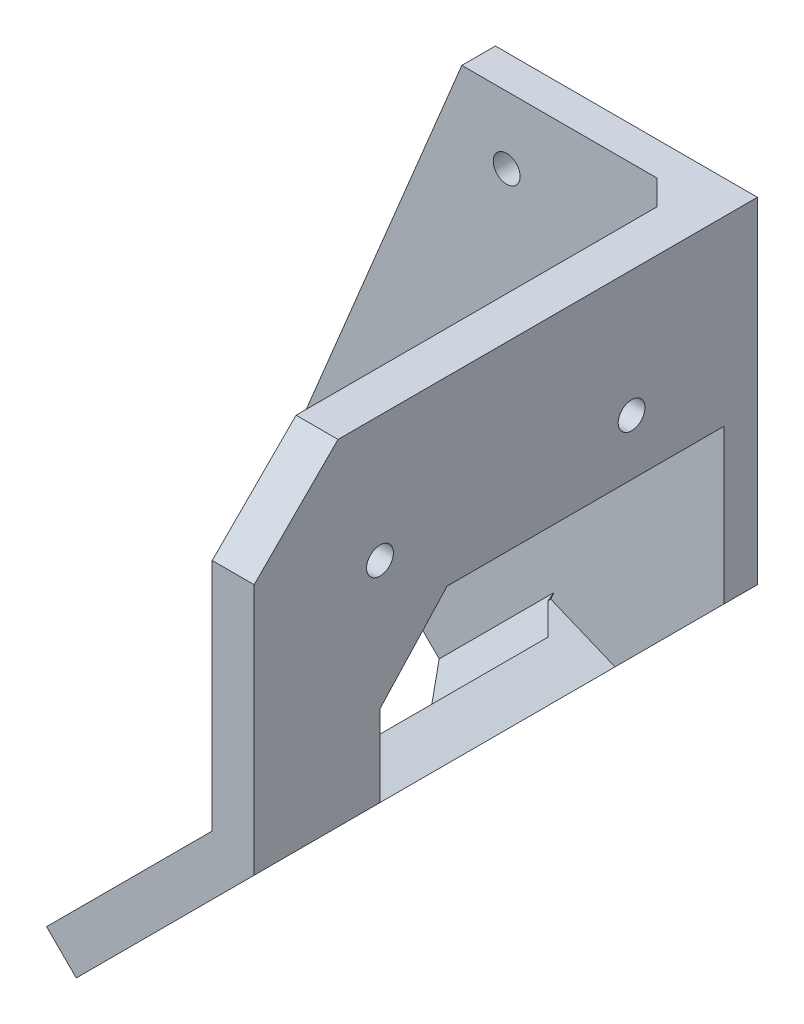
SolidWorks part; units mm, degrees
ref_plane "前视基准面" through (0, 0, 0) normal (0, 0, 1) x (1, 0, 0)
ref_plane "上视基准面" through (0, 0, 0) normal (0, 1, 0) x (1, 0, 0)
ref_plane "右视基准面" through (0, 0, 0) normal (1, 0, 0) x (0, 0, -1)
sketch "Sketch1" plane through (0, 0, 0) normal (0, 0, 1) x (1, 0, 0)
  line L0 (225, -175) -> (225, -135)
  line L2 (220, -135) -> (220, -172.9289)
  line L3 (220, -172.9289) -> (193.1802, -199.7487)
  line L5 (115, -285) -> (225, -175) construction
  line L6 (196.7157, -203.2843) -> (225, -175)
  line L7 (220, -135) -> (225, -135)
  line L8 (196.7157, -203.2843) -> (193.1802, -199.7487)
  dimension "D1" = 5
  dimension "D2" = 5
  dimension "D3" = 40
extrude "Boss-Extrude1" add sketch "Sketch1" along normal blind 60
sketch "Sketch2" plane through (0, 0, 0) normal (0, 0, -1) x (-1, 0, 0)
  line L0 (-225, -135) -> (-193.7596, -135)
  line L1 (-193.7596, -135) -> (-174.6254, -181.194)
  line L2 (-174.6254, -181.194) -> (-196.7157, -203.2843)
  line L3 (-196.7157, -203.2843) -> (-225, -175)
  line L4 (-225, -175) -> (-225, -135)
  line L5 (-225, -135) -> (-220, -135) construction
  circle A0 centre (-207.2895, -167.6641) radius 1.6 construction
  circle A1 centre (-184.0621, -179.3169) radius 1.6 construction
  circle A2 centre (-199.105, -143) radius 1.6 construction
  circle A3 centre (-207.2895, -167.6641) radius 1.6
  circle A4 centre (-184.0621, -179.3169) radius 1.6
  circle A5 centre (-199.105, -143) radius 1.6
  point P17 (-196.7157, -203.2843)
  point P19 (-225, -135)
  dimension "D1" = 50
extrude "Boss-Extrude2" add sketch "Sketch2" against normal blind 4
chamfer "Chamfer1" distance 3 angle 45 2 edges at (206.5901, -186.3388, 4) (220, -153.9645, 4)
sketch "Sketch3" plane through (225, 0, 0) normal (1, 0, 0) x (0, 0, -1)
  line L1 (-60, -175) -> (-60, -135) construction
  line L2 (-60, -135) -> (0, -135) construction
  circle A0 centre (-45, -150) radius 1.6
  circle A1 centre (-15, -150) radius 1.6
  dimension "D1" = 15
  dimension "D2" = 15
  dimension "D3" = 15
  dimension "D4" = 30
  dimension "D5" = 3.2
extrude "Cut-Extrude1" cut sketch "Sketch3" against normal blind 8
sketch "Sketch4" plane through (200, -200, 0) normal (0.7071, -0.7071, 0) x (0, 0, -1)
  line L1 (-60, -4.6447) -> (-60, 35.3553) construction
  line L2 (-60, -4.6447) -> (0, -4.6447) construction
  circle A0 centre (-45, 10.3553) radius 1.6
  circle A1 centre (-15, 10.3553) radius 1.6
  dimension "D1" = 15
  dimension "D2" = 15
  dimension "D3" = 15
  dimension "D4" = 30
  dimension "D5" = 3.2
extrude "Cut-Extrude2" cut sketch "Sketch4" against normal blind 8
chamfer "Chamfer2" distance 10 angle 45 2 edges at (222.5, -135, 60) (194.948, -201.5165, 60)
ref_plane "Plane1" through (239.7792, -99.3198, 0) normal (0.9239, -0.3827, 0) x (0, 0, -1)
sketch "Sketch5" plane through (239.7792, -99.3198, 0) normal (0.9239, -0.3827, 0) x (0, 0, -1)
  line L0 (-37, -58.62) -> (-45, -66.62)
  line L1 (-45, -66.62) -> (-45, -84.5303)
  line L2 (-45, -84.5303) -> (-37, -92.5303)
  line L3 (-37, -92.5303) -> (-4, -92.5303)
  line L4 (-4, -92.5303) -> (-4, -58.62)
  line L5 (-4, -58.62) -> (-37, -58.62)
  line L6 (-50, -38.62) -> (0, -38.62) construction
  line L7 (-50, -112.5303) -> (0, -112.5303) construction
  line L8 (-4, -75.5751) -> (-4, -41.6814) construction
  line L9 (-60, -75.5751) -> (-60, -47.8588) construction
  dimension "D1" = 20
  dimension "D2" = 20
  dimension "D3" = 15
  dimension "D4" = 8
  dimension "D5" = 45
extrude "Cut-Extrude3" cut sketch "Sketch5" along normal blind 40
